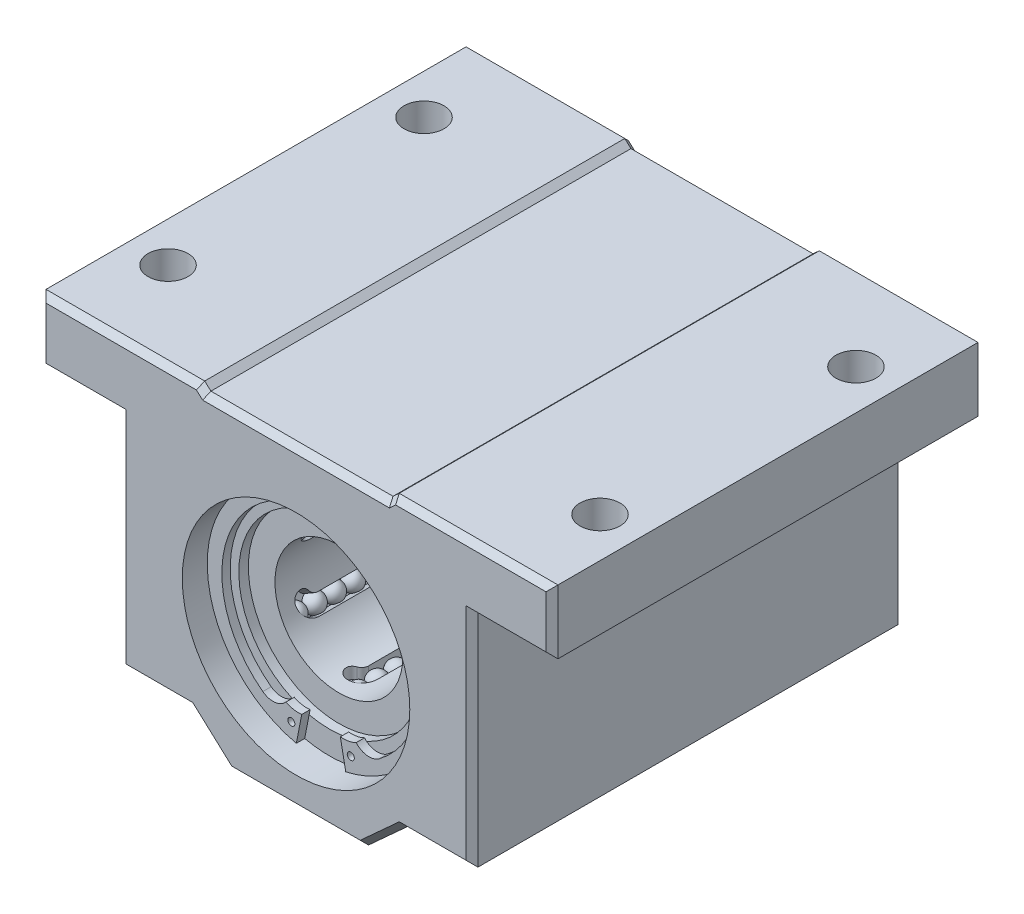
SolidWorks part; units mm, degrees
ref_plane "Front" through (0, 0, 0) normal (0, 0, 1) x (1, 0, 0)
ref_plane "Top" through (0, 0, 0) normal (0, 1, 0) x (1, 0, 0)
ref_plane "Right" through (0, 0, 0) normal (1, 0, 0) x (0, 0, -1)
sketch "Sketch1" plane through (0, 0, 0) normal (0, 0, 1) x (1, 0, 0)
  line L0 (0, 15.875) -> (0, -15.875) construction
  line L1 (-25.4, 15.875) -> (-9.652, 15.875)
  line L2 (-25.4, 15.875) -> (-25.4, 9.525)
  line L3 (-25.4, 9.525) -> (-17.4625, 9.525)
  line L4 (-17.4625, 9.525) -> (-17.4625, -12.3472)
  line L5 (-17.4625, -12.3472) -> (-10.4775, -12.3472)
  line L6 (-10.4775, -12.3472) -> (-6.6046, -15.875)
  line L7 (-6.6046, -15.875) -> (6.6046, -15.875)
  line L8 (-9.652, 15.875) -> (-9.036, 15.3106)
  line L9 (-9.036, 15.3106) -> (9.0361, 15.3106)
  line L10 (9.652, 15.875) -> (9.0361, 15.3106)
  line L11 (10.4775, -12.3472) -> (6.6046, -15.875)
  line L12 (17.4625, -12.3472) -> (10.4775, -12.3472)
  line L13 (17.4625, 9.525) -> (17.4625, -12.3472)
  line L14 (25.4, 9.525) -> (17.4625, 9.525)
  line L15 (25.4, 15.875) -> (25.4, 9.525)
  line L16 (25.4, 15.875) -> (9.652, 15.875)
  point P12 (0, 15.3106)
  dimension "F " = 31.75
  dimension "H" = 6.35
  dimension "Supplier M " = 34.925
  dimension "D " = 50.8
  dimension "D5" = 28.2222
  dimension "D6" = 5.2387
  dimension "D7" = 6.985
  dimension "D8" = 18.0721
  dimension "D9" = 0.5644
  dimension "D10" = 15.748
extrude "Extrude1" add sketch "Sketch1" along normal mid plane 42.8625
sketch "Sketch2" plane through (0, 0, 21.4312) normal (0, 0, 1) x (1, 0, 0)
  line L0 (-9.652, 15.875) -> (-25.4, 15.875) construction
  line L1 (0, -50) -> (0, 50) construction
  line L2 (0, -15.875) -> (0, -12.8764) construction
  line L3 (-6.6046, -15.875) -> (6.6046, -15.875) construction
  circle A0 centre (0, -1.5875) radius 11.2889
  dimension "D2" = 22.5778
  dimension "G" = 17.4625
extrude "Cut-Extrude1" cut sketch "Sketch2" against normal blind 3.3108
sketch "Sketch3" plane through (0, 0, 18.1205) normal (0, 0, 1) x (1, 0, 0)
  line L0 (-1.9168, -9.8612) -> (-2.4506, -12.6072)
  line L1 (0, -50) -> (0, 50) construction
  line L2 (0, 0) -> (0, 15.3106) construction
  line L3 (0, 0) -> (0, -12.8764) construction
  line L4 (1.9168, -9.8612) -> (2.4506, -12.6072)
  line L5 (0, 0) -> (-2.4506, -12.6072) construction
  line L6 (0, 0) -> (-2.9512, -11.0141) construction
  line L7 (9.0361, 15.3106) -> (-9.036, 15.3106) construction
  arc A0 (0, 8.4617) -> (-5.7785, -9.8213) centre (0.3175, -1.6933) ccw
  circle A1 centre (0, -1.5875) radius 9.8778 construction
  arc A2 (2.4506, -12.6072) -> (-2.4506, -12.6072) centre (0, -1.5875) ccw
  circle A3 centre (0, -1.5875) radius 11.2889 construction
  arc A4 (3.4859, -9.5792) -> (1.9168, -9.8612) centre (2.2225, -7.0556) cw
  arc A5 (5.7785, -9.8213) -> (3.4859, -9.5792) centre (4.7625, -8.4667) cw
  arc A6 (-5.7785, -9.8213) -> (-3.4859, -9.5792) centre (-4.7625, -8.4667) ccw
  arc A7 (-3.4859, -9.5792) -> (-1.9168, -9.8612) centre (-2.2225, -7.0556) ccw
  arc A9 (0, 8.4617) -> (5.7785, -9.8213) centre (-0.3175, -1.6933) cw
  circle A10 centre (-2.9512, -11.0141) radius 0.3528
  circle A11 centre (2.9512, -11.0141) radius 0.3528
  dimension "D1" = 10.16
  dimension "D4" = 1.6933
  dimension "D5" = 2.8222
  dimension "D8" = 0.7056
  dimension "D12" = 19.7556
  dimension "D2" = 1.6933
  dimension "D3" = 0.3175
  dimension "D6" = 11
  dimension "D7" = 15
  dimension "D9" = 7.0556
  dimension "D10" = 2.2225
  dimension "D11" = 8.4667
extrude "Extrude2" add sketch "Sketch3" along normal blind 0.8277
sketch "Sketch4" plane through (0, 0, 18.1205) normal (0, 0, 1) x (1, 0, 0)
  circle A0 centre (0, -1.5875) radius 8.9853
  circle A2 centre (0, -1.5875) radius 11.2889 construction
  dimension "D1" = 17.9705
extrude "Cut-Extrude2" cut sketch "Sketch4" against normal blind 0.9459
mirror "Mirror1" about plane through (0, 0, 0) normal (0, 0, 1) of "Cut-Extrude2", "Extrude2", "Cut-Extrude1"
sketch "Sketch5" plane through (0, 0, 17.1746) normal (0, 0, 1) x (1, 0, 0)
  circle A0 centre (0, -1.5875) radius 6.35
  circle A1 centre (0, -1.5875) radius 8.9853 construction
  dimension "ID " = 12.7
extrude "Cut-Extrude3" cut sketch "Sketch5" against normal through all
ref_plane "Plane1" through (0, -1.5875, 0) normal (0, 1, 0) x (-1, 0, 0)
sketch "Sketch8" plane through (0, -1.5875, 0) normal (0, 1, 0) x (-1, 0, 0)
  line L0 (-9.0361, 21.4312) -> (9.036, 21.4312) construction
  line L1 (0, 21.4312) -> (0, -21.4312) construction
  line L2 (0, 0) -> (-25.4, 0) construction
  line L3 (-25.4, 21.4312) -> (-25.4, -21.4312) construction
  line L4 (-0.8033, -14.0412) -> (-0.8033, 14.0412)
  line L5 (0.8033, -13.4134) -> (0.8033, 13.4134)
  line L6 (-0.8033, 14.0412) -> (0.8033, 14.0412) construction
  line L7 (0.8033, 15.6477) -> (0.8033, 14.0412) construction
  line L8 (0.8033, -15.6477) -> (0.8033, -14.0412) construction
  line L9 (-0.8033, -14.0412) -> (0.8033, -14.0412) construction
  arc A6 (-0.8033, 14.0412) -> (0.8033, 15.6477) centre (0.8033, 14.0412) cw
  arc A7 (1.2216, 14.1587) -> (0.8033, 15.6477) centre (0.8033, 14.8444) ccw
  arc A8 (1.2216, 14.1587) -> (0.8033, 13.4134) centre (1.6764, 13.4134) ccw
  arc A9 (1.2216, -14.1587) -> (0.8033, -13.4134) centre (1.6764, -13.4134) cw
  arc A10 (1.2216, -14.1587) -> (0.8033, -15.6477) centre (0.8033, -14.8444) cw
  arc A11 (-0.8033, -14.0412) -> (0.8033, -15.6477) centre (0.8033, -14.0412) ccw
  point P10 (-0.8033, 0)
  point P41 (0.8033, 0)
  dimension "D5" = 0.8731
  dimension "D6" = 1.6065
  dimension "D1" = 7.3901
  dimension "D2" = 1.6065
extrude "Cut-Extrude4" cut sketch "Sketch8" against normal offset from surface (7.4356 mm away) 1.1289
pattern_circular "CirPattern1" count 6 over 360 about axis through (0, -1.5875, 0) along (0, 0, 1) of "Cut-Extrude4"
sketch "Sketch10" plane through (0, 0, 0) normal (0, 0, 1) x (1, 0, 0)
  line L0 (-0.8033, -7.8865) -> (-0.8033, -9.0231) construction
  line L1 (0.8033, -7.8865) -> (0.8033, -9.0231) construction
  line L2 (-0.8033, -9.0231) -> (0.8033, -9.0231) construction
  line L3 (-0.9488, -8.8863) -> (0.9488, -8.8863)
  circle A0 centre (0, -1.5875) radius 6.35 construction
  circle A2 centre (0, -1.5875) radius 6.35 construction
  arc A3 (0.9488, -8.8863) -> (-0.9488, -8.8863) centre (0, -8.8863) ccw
  dimension "D1" = 0.1455
  dimension "D2" = 0.1455
revolve "Revolve2" add sketch "Sketch10" angle 360 about L3
pattern_linear "LPattern1" count 9 spacing 1.905 along (0, 0, 1) of "Revolve2"
mirror "Mirror2" about plane through (0, 0, 0) normal (0, 0, 1) of "Revolve2", "LPattern1"
pattern_circular "CirPattern2" count 6 over 360 about axis through (0, -1.5875, 0) along (0, 0, 1) of "Revolve2", "Mirror2", "LPattern1"
chamfer "Chamfer1" distance 0.5912 angle 45 32 edges at (17.4625, -1.4111, -21.4312) (13.97, -12.3472, -21.4312) (8.5411, -14.1111, -21.4312) (0, -15.875, -21.4312) (-8.5411, -14.1111, -21.4312) (-13.97, -12.3472, -21.4312) (-17.4625, -1.4111, -21.4312) (-21.4312, 9.525, -21.4312) (-25.4, 12.7, -21.4312) (-17.526, 15.875, -21.4312) (-9.344, 15.5928, -21.4312) (0, 15.3106, -21.4312) (9.344, 15.5928, -21.4312) (17.526, 15.875, -21.4312) (25.4, 12.7, -21.4312) (21.4312, 9.525, -21.4312) (9.344, 15.5928, 21.4312) (0, 15.3106, 21.4312) (-9.344, 15.5928, 21.4312) (-17.526, 15.875, 21.4312) (-25.4, 12.7, 21.4312) (-21.4312, 9.525, 21.4312) (-17.4625, -1.4111, 21.4312) (-13.97, -12.3472, 21.4312) (-8.5411, -14.1111, 21.4312) (0, -15.875, 21.4312) (8.5411, -14.1111, 21.4312) (13.97, -12.3472, 21.4312) (17.4625, -1.4111, 21.4312) (21.4312, 9.525, 21.4312) (25.4, 12.7, 21.4312) (17.526, 15.875, 21.4312)
sketch "Sketch13" plane through (0, 15.875, 0) normal (0, 1, 0) x (1, 0, 0)
  line L0 (21.4313, 0) -> (-21.4312, 0) construction
  line L1 (-21.4312, 12.7) -> (21.4312, 12.7) construction
  line L2 (-21.4312, 12.7) -> (-21.4312, -12.7) construction
  line L3 (-21.4312, -12.7) -> (21.4313, -12.7) construction
  line L4 (21.4312, 12.7) -> (21.4313, -12.7) construction
  line L6 (0, 12.7) -> (0, -12.7) construction
  circle A0 centre (-21.4312, 12.7) radius 1.9844
  circle A1 centre (21.4312, 12.7) radius 1.9844
  circle A2 centre (21.4313, -12.7) radius 1.9844
  circle A3 centre (-21.4312, -12.7) radius 1.9844
  dimension "L " = 3.9688
  dimension "K " = 25.4
  dimension "J " = 42.8625
extrude "Cut-Extrude6" cut sketch "Sketch13" against normal up to surface (6.35 mm away) up to face at (21.4312, 9.525, 0)
equation "\"D5@Sketch1\" = \"F @Sketch1\" * .888888888889"
equation "\"D9@Sketch1\" = \"F @Sketch1\" * .017777777778"
equation "\"D7@Sketch1\" = \"Supplier M @Sketch1\" * .2"
equation "\"D6@Sketch1\" = \"Supplier M @Sketch1\" * .15"
equation "\"D10@Sketch1\" = \"D @Sketch1\" * .31"
equation "\"D8@Sketch1\" = \"D @Sketch1\" * .35575"
equation "\"D1@Cut-Extrude1\" = \"B @Extrude1\" * .0772413793"
equation "\"D2@Sketch2\" = \"F @Sketch1\" * .71111111111"
equation "\"D3@Sketch3\" = \"D10@Sketch3\" * .1428571429"
equation "\"D1@Sketch3\" = \"D12@Sketch3\" * .5142857143"
equation "\"D2@Sketch3\" = \"D12@Sketch3\" * .0857142857"
equation "\"D11@Sketch3\" = \"D12@Sketch3\" * .4285714286"
equation "\"D9@Sketch3\" = \"D12@Sketch3\" * .3571428571"
equation "\"D4@Sketch3\" = \"D12@Sketch3\" * .0857142857"
equation "\"D8@Sketch3\" = \"D12@Sketch3\" * .0357142857"
equation "\"D5@Sketch3\" = \"D12@Sketch3\" * .1428571429"
equation "\"D10@Sketch3\" = \"D @Sketch1\" * .04375"
equation "\"D12@Sketch3\" = \"F @Sketch1\" * .6222222222"
equation "\"D1@Extrude2\" = \"B @Extrude1\" * .0193103448"
equation "\"D1@Sketch4\" = \"D @Sketch1\" * .35375"
equation "\"D1@Cut-Extrude2\" = \"B @Extrude1\" * .0220689655"
equation "\"D1@Sketch8\" = \"B @Extrude1\" * .1724137931"
equation "\"D1@Cut-Extrude4\" = \"F @Sketch1\" * .0355555555556"
equation "\"D2@Sketch8\" = \"Supplier M @Sketch1\" * .046"
equation "\"D6@Sketch8\" = \"Supplier M @Sketch1\" * .046"
equation "\"D5@Sketch8\" = \"Supplier M @Sketch1\" * .025"
equation "\"D2@Sketch10\" = \"D1@Sketch10\""
equation "\"D1@Sketch10\" = \"Supplier M @Sketch1\" * .00416666667"
equation "\"D1@Chamfer1\" = \"B @Extrude1\" * .0137931034"
